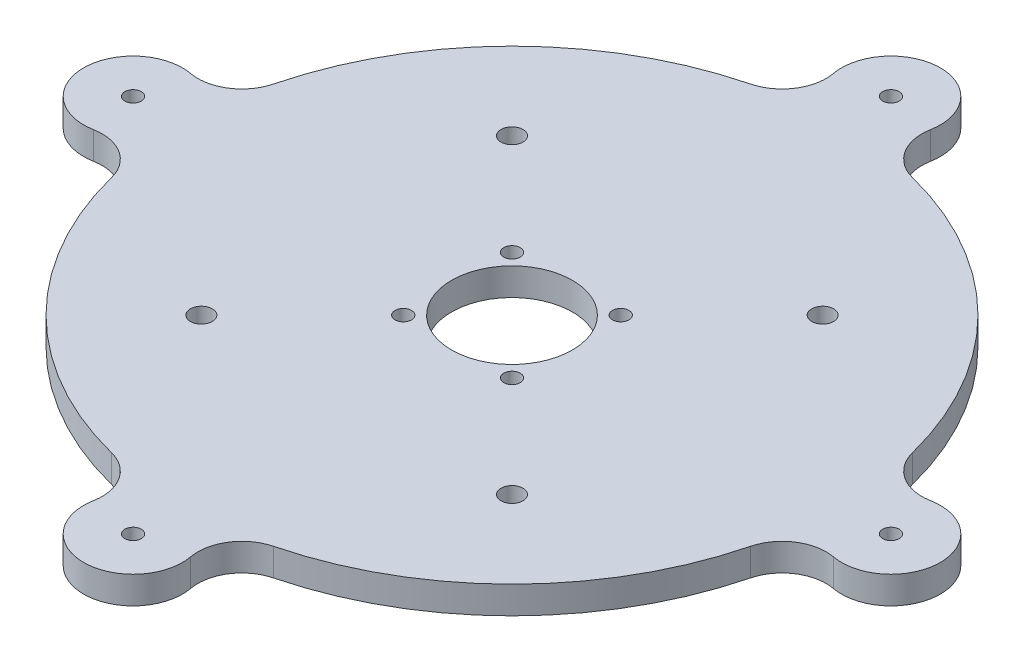
SolidWorks part; units mm, degrees
ref_plane "Front Plane" through (0, 0, 0) normal (0, 0, 1) x (1, 0, 0)
ref_plane "Top Plane" through (0, 0, 0) normal (0, 1, 0) x (1, 0, 0)
ref_plane "Right Plane" through (0, 0, 0) normal (1, 0, 0) x (0, 0, -1)
sketch "Sketch1" plane through (0, 0, 0) normal (0, 1, 0) x (1, 0, 0)
  line L0 (0, 0) -> (14, 0) construction
  line L1 (0, 0) -> (9.8995, 9.8995) construction
  line L2 (9.8995, 9.8995) -> (28.2843, 28.2843) construction
  line L3 (0, 0) -> (40, 0) construction
  arc A37 (-58.1586, -14.7506) -> (-14.7506, -58.1586) centre (0, 0) ccw
  circle A38 centre (0, 0) radius 11
  circle A39 centre (0, 0) radius 14 construction
  circle A40 centre (9.8995, 9.8995) radius 1.5
  arc A42 (-58.1586, -14.7506) -> (-14.7506, -58.1586) centre (0, 0) ccw
  circle A43 centre (9.8995, -9.8995) radius 1.5
  arc A44 (-58.1586, -14.7506) -> (-14.7506, -58.1586) centre (0, 0) ccw
  circle A45 centre (-9.8995, -9.8995) radius 1.5
  arc A46 (-58.1586, -14.7506) -> (-14.7506, -58.1586) centre (0, 0) ccw
  circle A47 centre (-9.8995, 9.8995) radius 1.5
  circle A48 centre (0, 0) radius 40 construction
  circle A49 centre (28.2843, 28.2843) radius 2
  arc A50 (-58.1586, -14.7506) -> (-14.7506, -58.1586) centre (0, 0) ccw
  circle A51 centre (28.2843, -28.2843) radius 2
  arc A52 (-58.1586, -14.7506) -> (-14.7506, -58.1586) centre (0, 0) ccw
  circle A53 centre (-28.2843, -28.2843) radius 2
  arc A54 (-58.1586, -14.7506) -> (-14.7506, -58.1586) centre (0, 0) ccw
  circle A55 centre (-28.2843, 28.2843) radius 2
  arc A57 (67.3657, -8.8504) -> (67.3657, 8.8504) centre (69, 0) ccw
  arc A58 (-14.7506, 58.1586) -> (-58.1586, 14.7506) centre (0, 0) ccw
  arc A59 (-8.8504, -67.3657) -> (8.8504, -67.3657) centre (0, -69) ccw
  arc A60 (-14.7506, 58.1586) -> (-58.1586, 14.7506) centre (0, 0) ccw
  arc A61 (-67.3657, 8.8504) -> (-67.3657, -8.8504) centre (-69, 0) ccw
  arc A62 (-14.7506, 58.1586) -> (-58.1586, 14.7506) centre (0, 0) ccw
  arc A63 (8.8504, 67.3657) -> (-8.8504, 67.3657) centre (0, 69) ccw
  arc A65 (58.1586, 14.7506) -> (67.3657, 8.8504) centre (65.913, 16.7174) ccw
  arc A66 (-58.1586, -14.7506) -> (-14.7506, -58.1586) centre (0, 0) ccw
  arc A67 (14.7506, -58.1586) -> (8.8504, -67.3657) centre (16.7174, -65.913) ccw
  arc A68 (-58.1586, -14.7506) -> (-14.7506, -58.1586) centre (0, 0) ccw
  arc A69 (-58.1586, -14.7506) -> (-67.3657, -8.8504) centre (-65.913, -16.7174) ccw
  arc A70 (-58.1586, -14.7506) -> (-14.7506, -58.1586) centre (0, 0) ccw
  arc A71 (-14.7506, 58.1586) -> (-8.8504, 67.3657) centre (-16.7174, 65.913) ccw
  arc A72 (67.3657, -8.8504) -> (58.1586, -14.7506) centre (65.913, -16.7174) ccw
  arc A73 (-58.1586, -14.7506) -> (-14.7506, -58.1586) centre (0, 0) ccw
  arc A74 (-8.8504, -67.3657) -> (-14.7506, -58.1586) centre (-16.7174, -65.913) ccw
  arc A75 (-58.1586, -14.7506) -> (-14.7506, -58.1586) centre (0, 0) ccw
  arc A76 (-67.3657, 8.8504) -> (-58.1586, 14.7506) centre (-65.913, 16.7174) ccw
  arc A77 (-58.1586, -14.7506) -> (-14.7506, -58.1586) centre (0, 0) ccw
  arc A78 (8.8504, 67.3657) -> (14.7506, 58.1586) centre (16.7174, 65.913) ccw
  arc A79 (-14.7506, 58.1586) -> (-58.1586, 14.7506) centre (0, 0) ccw
  arc A80 (-14.7506, 58.1586) -> (-58.1586, 14.7506) centre (0, 0) ccw
  arc A81 (-14.7506, 58.1586) -> (-58.1586, 14.7506) centre (0, 0) ccw
  arc A82 (-14.7506, 58.1586) -> (-58.1586, 14.7506) centre (0, 0) ccw
  arc A83 (-14.7506, 58.1586) -> (-58.1586, 14.7506) centre (0, 0) ccw
  arc A84 (-14.7506, 58.1586) -> (-58.1586, 14.7506) centre (0, 0) ccw
  arc A85 (-14.7506, 58.1586) -> (-58.1586, 14.7506) centre (0, 0) ccw
  arc A86 (-14.7506, 58.1586) -> (-58.1586, 14.7506) centre (0, 0) ccw
  arc A87 (-14.7506, 58.1586) -> (-58.1586, 14.7506) centre (0, 0) ccw
  arc A88 (-14.7506, 58.1586) -> (-58.1586, 14.7506) centre (0, 0) ccw
  arc A89 (58.1586, 14.7506) -> (14.7506, 58.1586) centre (0, 0) ccw
  arc A90 (58.1586, 14.7506) -> (14.7506, 58.1586) centre (0, 0) ccw
  arc A91 (58.1586, 14.7506) -> (14.7506, 58.1586) centre (0, 0) ccw
  arc A92 (58.1586, 14.7506) -> (14.7506, 58.1586) centre (0, 0) ccw
  arc A93 (58.1586, 14.7506) -> (14.7506, 58.1586) centre (0, 0) ccw
  arc A94 (58.1586, 14.7506) -> (14.7506, 58.1586) centre (0, 0) ccw
  arc A95 (58.1586, 14.7506) -> (14.7506, 58.1586) centre (0, 0) ccw
  arc A96 (58.1586, 14.7506) -> (14.7506, 58.1586) centre (0, 0) ccw
  arc A97 (58.1586, 14.7506) -> (14.7506, 58.1586) centre (0, 0) ccw
  arc A98 (58.1586, 14.7506) -> (14.7506, 58.1586) centre (0, 0) ccw
  arc A99 (58.1586, 14.7506) -> (14.7506, 58.1586) centre (0, 0) ccw
  arc A100 (58.1586, 14.7506) -> (14.7506, 58.1586) centre (0, 0) ccw
  arc A101 (58.1586, 14.7506) -> (14.7506, 58.1586) centre (0, 0) ccw
  arc A102 (14.7506, -58.1586) -> (58.1586, -14.7506) centre (0, 0) ccw
  arc A103 (14.7506, -58.1586) -> (58.1586, -14.7506) centre (0, 0) ccw
  arc A104 (14.7506, -58.1586) -> (58.1586, -14.7506) centre (0, 0) ccw
  arc A105 (14.7506, -58.1586) -> (58.1586, -14.7506) centre (0, 0) ccw
  arc A106 (14.7506, -58.1586) -> (58.1586, -14.7506) centre (0, 0) ccw
  arc A107 (14.7506, -58.1586) -> (58.1586, -14.7506) centre (0, 0) ccw
  arc A108 (14.7506, -58.1586) -> (58.1586, -14.7506) centre (0, 0) ccw
  arc A109 (14.7506, -58.1586) -> (58.1586, -14.7506) centre (0, 0) ccw
  arc A110 (14.7506, -58.1586) -> (58.1586, -14.7506) centre (0, 0) ccw
  arc A111 (14.7506, -58.1586) -> (58.1586, -14.7506) centre (0, 0) ccw
  arc A112 (14.7506, -58.1586) -> (58.1586, -14.7506) centre (0, 0) ccw
  arc A113 (14.7506, -58.1586) -> (58.1586, -14.7506) centre (0, 0) ccw
  arc A114 (14.7506, -58.1586) -> (58.1586, -14.7506) centre (0, 0) ccw
  circle A115 centre (69, 0) radius 1.5
  circle A116 centre (0, 69) radius 1.5
  circle A117 centre (-69, 0) radius 1.5
  circle A119 centre (0, -69) radius 1.5
  point P23 (0, 0)
  point P35 (0, 0)
  point P36 (14.7506, -58.1586)
  point P49 (0, 0)
  point P51 (-18.0814, -57.2107)
  point P55 (0, -60)
  point P57 (-14.5507, -58.212)
  point P58 (14.7506, -58.1586)
  point P61 (0, 0)
  point P62 (-14.7506, -58.1586)
  point P63 (0, 0)
  point P64 (-14.7506, -58.1586)
  point P66 (0, 0)
  point P73 (0, 0)
  dimension "D1" = 120
  dimension "D2" = 22
  dimension "D3" = 28
  dimension "D5" = 45
  dimension "D7" = 80
  dimension "D8" = 4
  dimension "D9" = 3
  dimension "D10" = 18
  dimension "D11" = 4
  dimension "D12" = 4
  dimension "D13" = 16
  dimension "D14" = 16
  dimension "D15" = 4
  dimension "D16" = 3
  dimension "D17" = 3
  dimension "D18" = 69
  dimension "D19" = 3
  dimension "D4" = 3
  dimension "D20" = 65.913
  dimension "D6" = 4
  dimension "D21" = 58.1586
  dimension "D22" = 67.3657
  dimension "D23" = 65.913
extrude "Boss-Extrude1" add sketch "Sketch1" along normal blind 5 contours A67 A102 A72 A57 A65 A89 A78 A63 A71 A58 A76 A61 A69 A37 A74 A59 A119 A117 A116 A115 A38 A40 A43 A45 A47 A49 A51 A53 A55
